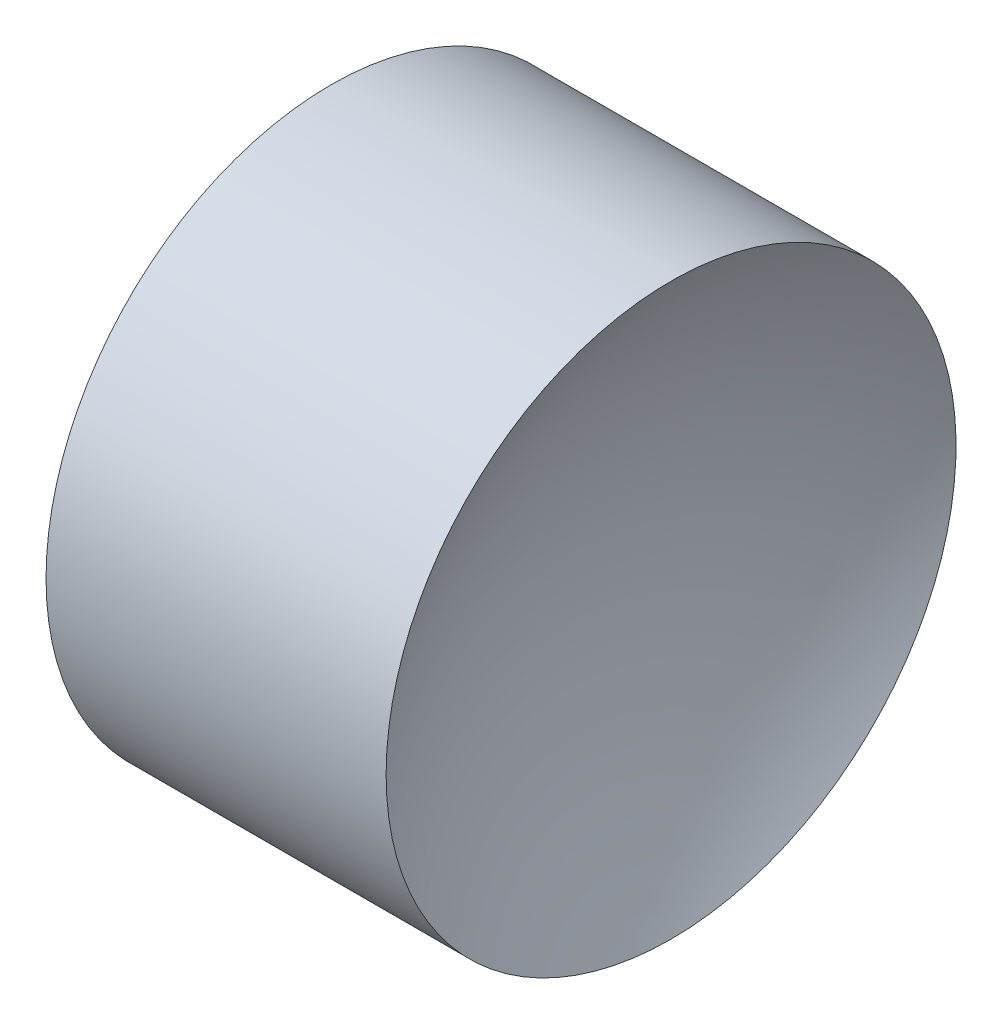
SolidWorks part; units mm, degrees
ref_plane "前视基准面" through (0, 0, 0) normal (0, 0, 1) x (1, 0, 0)
ref_plane "上视基准面" through (0, 0, 0) normal (0, 1, 0) x (1, 0, 0)
ref_plane "右视基准面" through (0, 0, 0) normal (1, 0, 0) x (0, 0, -1)
sketch "草图2" plane through (0, 0, 0) normal (0, 0, 1) x (1, 0, 0)
  line L0 (21.2249, 13.0445) -> (27.8323, 13.0445) construction
  line L1 (23.0119, 13.0445) -> (25.0119, 13.0445)
  line L3 (24.0119, 16.1945) -> (22.1322, 16.1945)
  line L4 (24.0119, 16.1945) -> (25.8915, 16.1945)
  arc A0 (23.0119, 13.0445) -> (22.1322, 16.1945) centre (16.9319, 13.0445) ccw
  arc A1 (25.8915, 16.1945) -> (25.0119, 13.0445) centre (31.0919, 13.0445) ccw
revolve "旋转1" add sketch "草图2" angle 360 about L0
